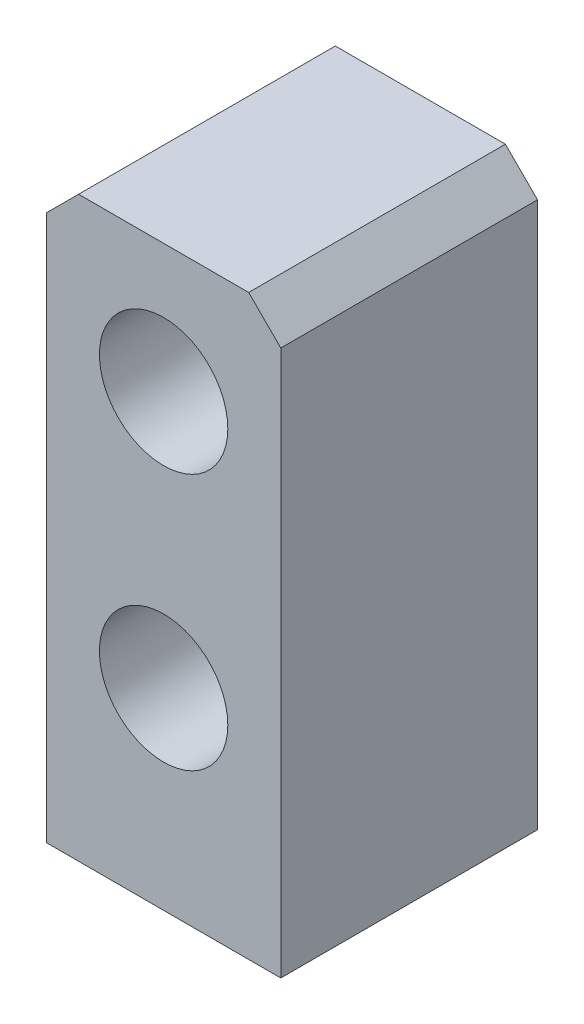
SolidWorks part; units mm, degrees
ref_plane "Alzado" through (0, 0, 0) normal (0, 0, 1) x (1, 0, 0)
ref_plane "Planta" through (0, 0, 0) normal (0, 1, 0) x (1, 0, 0)
ref_plane "Vista lateral" through (0, 0, 0) normal (1, 0, 0) x (0, 0, -1)
sketch "Croquis1" plane through (0, 0, 0) normal (0, 0, 1) x (1, 0, 0)
  line L0 (-18.25, 40) -> (-13.25, 45)
  line L1 (-18.25, -45) -> (18.25, -45)
  line L2 (-18.25, -45) -> (-18.25, 40)
  line L3 (-13.25, 45) -> (13.25, 45)
  line L4 (18.25, -45) -> (18.25, 40)
  line L5 (-18.25, -45) -> (18.25, 45) construction
  line L6 (-18.25, 45) -> (18.25, -45) construction
  line L7 (13.25, 45) -> (18.25, 40)
  point P0 (0, 0)
  dimension "D1" = 90
  dimension "D2" = 36.5
extrude "Saliente-Extruir1" add sketch "Croquis1" along normal blind 40
sketch "Croquis2" plane through (0, 0, 40) normal (0, 0, 1) x (1, 0, 0)
  line L0 (0, 46.7298) -> (0, -49.2298) construction
  line L1 (-18.25, -45) -> (18.25, -45) construction
  circle A0 centre (0, 25) radius 10
  circle A1 centre (0, -15) radius 10
  dimension "D1" = 20
  dimension "D2" = 20
  dimension "D3" = 40
  dimension "D4" = 30
extrude "Cortar-Extruir1" cut sketch "Croquis2" against normal blind 40
